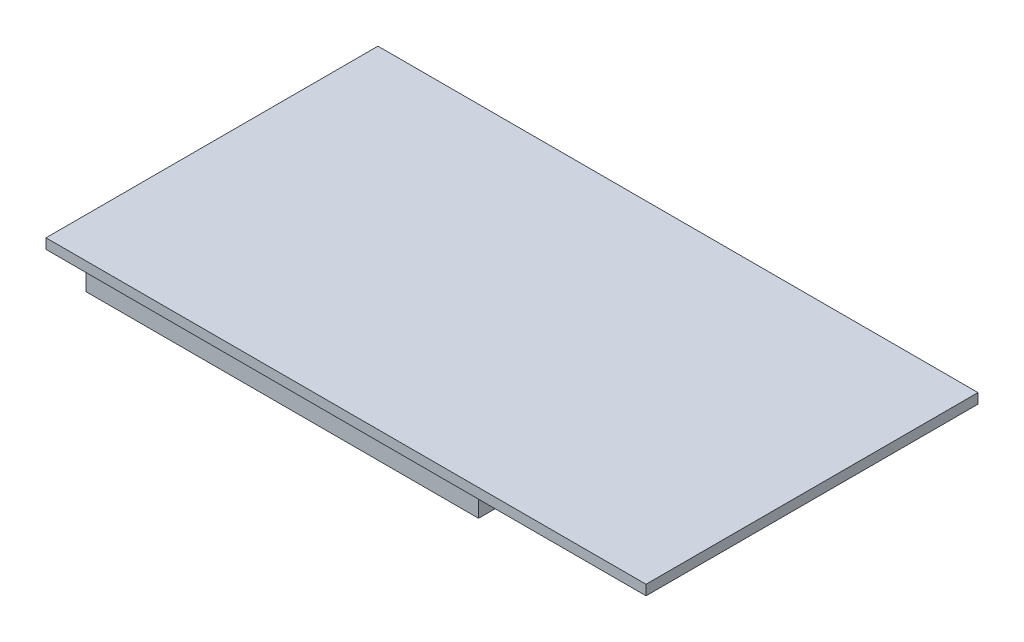
SolidWorks part; units mm, degrees
ref_plane "Спереди" through (0, 0, 0) normal (0, 0, 1) x (1, 0, 0)
ref_plane "Сверху" through (0, 0, 0) normal (0, 1, 0) x (1, 0, 0)
ref_plane "Справа" through (0, 0, 0) normal (1, 0, 0) x (0, 0, -1)
sketch "Эскиз1" plane through (0, 0, 0) normal (0, 1, 0) x (1, 0, 0)
  line L0 (0, 0) -> (119.3, 0)
  line L1 (0, 0) -> (0, 66)
  line L2 (119.3, 0) -> (119.3, 66)
  line L3 (0, 66) -> (119.3, 66)
  dimension "D1" = 66
  dimension "D2" = 119.3
extrude "Бобышка-Вытянуть1" add sketch "Эскиз1" along normal blind 2
sketch "Эскиз2" plane through (0, 0, 0) normal (0, -1, 0) x (1, 0, 0)
  line L0 (1, -7) -> (1, -12)
  line L1 (1, -7) -> (79, -7)
  line L2 (1, -12) -> (79, -12)
  line L3 (79, -7) -> (79, -12)
  line L4 (0, -33) -> (119.3, -33) construction
  line L5 (0, -66) -> (0, 0) construction
  line L6 (119.3, 0) -> (119.3, -66) construction
  line L7 (0, 0) -> (119.3, 0) construction
  line L8 (79, -59) -> (79, -54)
  line L9 (1, -54) -> (79, -54)
  line L10 (1, -59) -> (79, -59)
  line L11 (1, -59) -> (1, -54)
  dimension "D1" = 78
  dimension "D2" = 5
  dimension "D3" = 1
  dimension "D4" = 7
extrude "Бобышка-Вытянуть2" add sketch "Эскиз2" along normal blind 10.3
sketch "Эскиз3" plane through (0, 0, 0) normal (-1, 0, 0) x (0, 0, 1)
  line L0 (-29.5, 0) -> (-36.5, 0)
  line L1 (-29.5, 0) -> (-29.5, -3)
  line L2 (-36.5, 0) -> (-36.5, -3)
  line L3 (-29.5, -3) -> (-36.5, -3)
  line L4 (-66, 0) -> (0, 0) construction
  line L5 (-33, 0) -> (-33, -3) construction
  line L6 (-33, 0) -> (-33, -3) construction
  line L7 (-36, -0.5) -> (-30, -0.5)
  line L8 (-36, -0.5) -> (-36, -2.5)
  line L9 (-30, -0.5) -> (-30, -2.5)
  line L10 (-36, -2.5) -> (-30, -2.5)
  dimension "D1" = 7
  dimension "D2" = 3
  dimension "D3" = 0.5
  dimension "D4" = 0.5
  dimension "D5" = 0.5
  dimension "D6" = 0.5
extrude "Бобышка-Вытянуть3" add sketch "Эскиз3" against normal blind 10
sketch "Эскиз4" plane through (0, 2, 0) normal (0, 1, 0) x (1, 0, 0)
  line L0 (119.3, 33) -> (0, 33) construction
  line L1 (119.3, 0) -> (119.3, 66) construction
  line L2 (0, 66) -> (0, 0) construction
